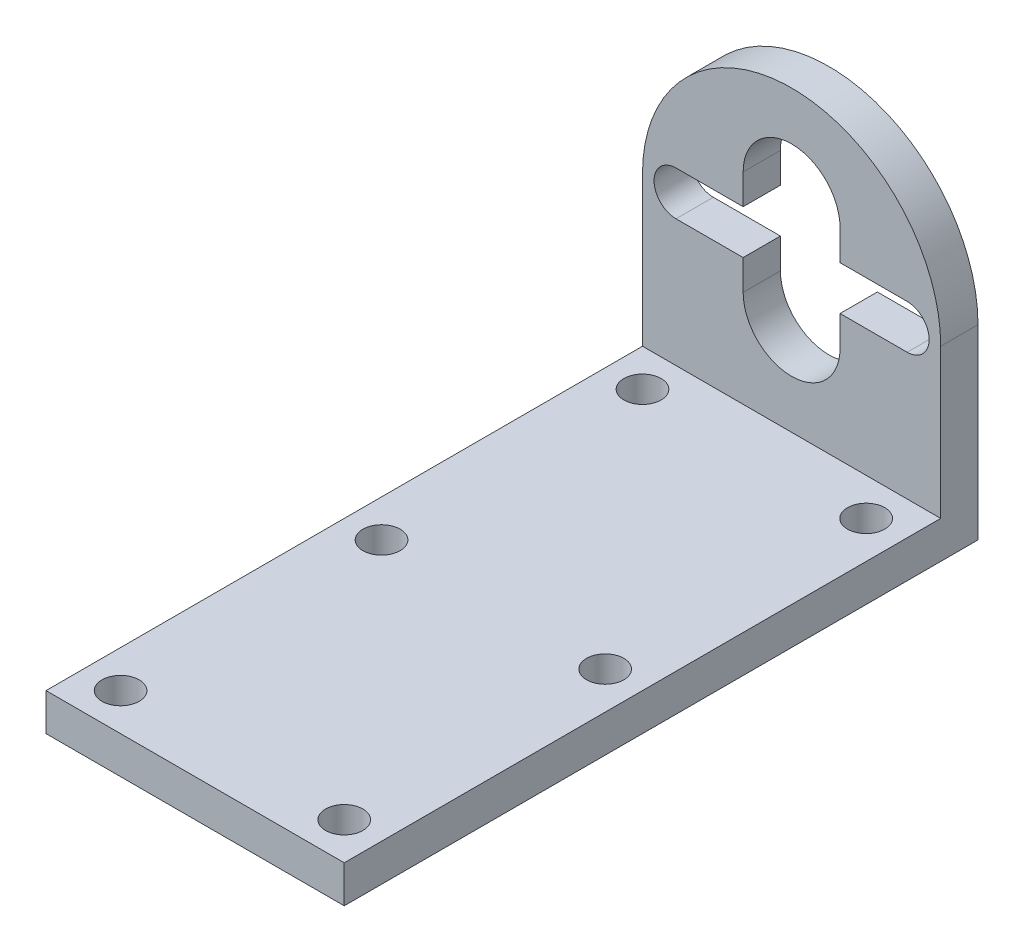
SolidWorks part; units mm, degrees
material "5052-H34"
ref_plane "Front Plane" through (0, 0, 0) normal (0, 0, 1) x (1, 0, 0)
ref_plane "Top Plane" through (0, 0, 0) normal (0, 1, 0) x (1, 0, 0)
ref_plane "Right Plane" through (0, 0, 0) normal (1, 0, 0) x (0, 0, -1)
sketch "Sketch2" plane through (0, 0, 0) normal (0, 0, 1) x (1, 0, 0)
  line L0 (20, 0) -> (20, -25)
  line L1 (20, -25) -> (-20, -25)
  line L2 (-20, -25) -> (-20, 0)
  line L3 (-15.5, 0) -> (15.5, 0) construction
  line L6 (-15.5, 2.95) -> (15.5, 2.95)
  line L7 (-15.5, -2.95) -> (15.5, -2.95)
  arc A0 (20, 0) -> (-20, 0) centre (0, 0) ccw
  arc A3 (-15.5, 2.95) -> (-15.5, -2.95) centre (-15.5, 0) ccw
  arc A4 (15.5, -2.95) -> (15.5, 2.95) centre (15.5, 0) ccw
  point P8 (0, 0)
  dimension "D1" = 40
  dimension "D4" = 2.95
  dimension "D2" = 25
  dimension "D3" = 31
extrude "Boss-Extrude1" add sketch "Sketch2" along normal blind 5
sketch "Sketch3" plane through (0, 0, 5) normal (0, 0, 1) x (1, 0, 0)
  line L0 (20, -25) -> (20, 0) construction
  line L1 (20, -20) -> (-20, -20)
  line L2 (20, -20) -> (20, -25)
  line L3 (20, -25) -> (-20, -25)
  line L4 (-20, -20) -> (-20, -25)
  dimension "D1" = 5
extrude "Boss-Extrude2" add sketch "Sketch3" along normal blind 80
sketch "Sketch4" plane through (0, -20, 0) normal (0, 1, 0) x (1, 0, 0)
  line L0 (0, 0) -> (0, -85) construction
  line L1 (20, -85) -> (-20, -85) construction
  line L2 (20, -85) -> (20, -5) construction
  line L3 (-15, -10) -> (15, -10) construction
  line L4 (-15, -10) -> (-15, -80) construction
  line L5 (-15, -80) -> (15, -80) construction
  line L6 (15, -10) -> (15, -80) construction
  line L7 (-20, -85) -> (-20, -5) construction
  line L8 (-20, -5) -> (20, -5) construction
  circle A0 centre (-15, -10) radius 2.5
  circle A1 centre (15, -10) radius 2.5
  circle A2 centre (15, -80) radius 2.5
  circle A3 centre (-15, -80) radius 2.5
  circle A4 centre (-15, -45) radius 2.5
  circle A5 centre (15, -45) radius 2.5
  dimension "D5" = 5
  dimension "D1" = 5
  dimension "D2" = 5
  dimension "D3" = 5
  dimension "D4" = 5
extrude "Cut-Extrude1" cut sketch "Sketch4" against normal blind 10
sketch "Sketch5" plane through (0, 0, 5) normal (0, 0, 1) x (1, 0, 0)
  line L0 (0, 7) -> (0, -7) construction
  line L5 (6.5, 7) -> (6.5, -7)
  line L9 (-6.5, 7) -> (-6.5, -7)
  arc A6 (6.5, 7) -> (-6.5, 7) centre (0, 7) ccw
  arc A7 (-6.5, -7) -> (6.5, -7) centre (0, -7) ccw
  point P2 (0, 0)
  dimension "D1" = 14
  dimension "D2" = 6.5
extrude "Cut-Extrude2" cut sketch "Sketch5" against normal blind 10
